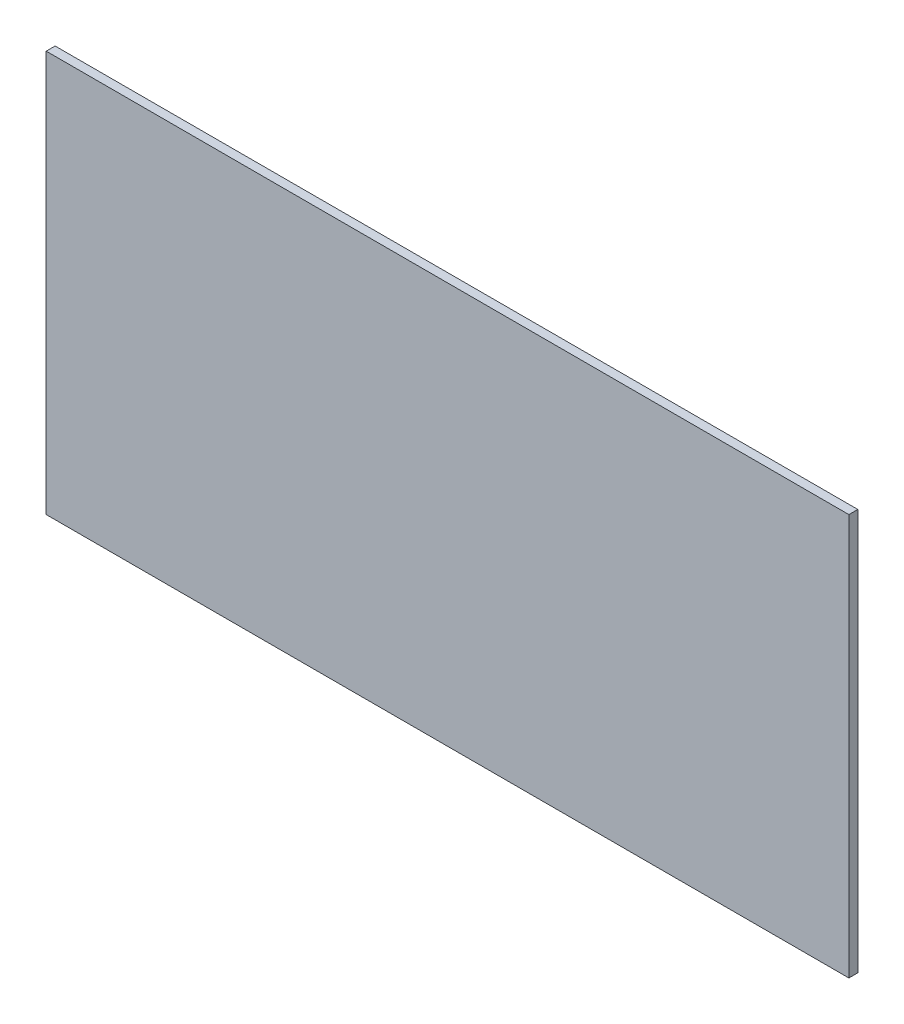
SolidWorks part; units mm, degrees
ref_plane "前视基准面" through (0, 0, 0) normal (0, 0, 1) x (1, 0, 0)
ref_plane "上视基准面" through (0, 0, 0) normal (0, 1, 0) x (1, 0, 0)
ref_plane "右视基准面" through (0, 0, 0) normal (1, 0, 0) x (0, 0, -1)
sketch "草图1" plane through (0, 0, 0) normal (0, 0, 1) x (1, 0, 0)
  line L1 (-90, -45) -> (90, -45)
  line L2 (-90, -45) -> (-90, 45)
  line L3 (-90, 45) -> (90, 45)
  line L4 (90, -45) -> (90, 45)
  line L5 (-90, -45) -> (90, 45) construction
  line L6 (-90, 45) -> (90, -45) construction
  point P0 (0, 0)
  dimension "D1" = 180
  dimension "D2" = 90
extrude "凸台-拉伸1" add sketch "草图1" along normal blind 2
